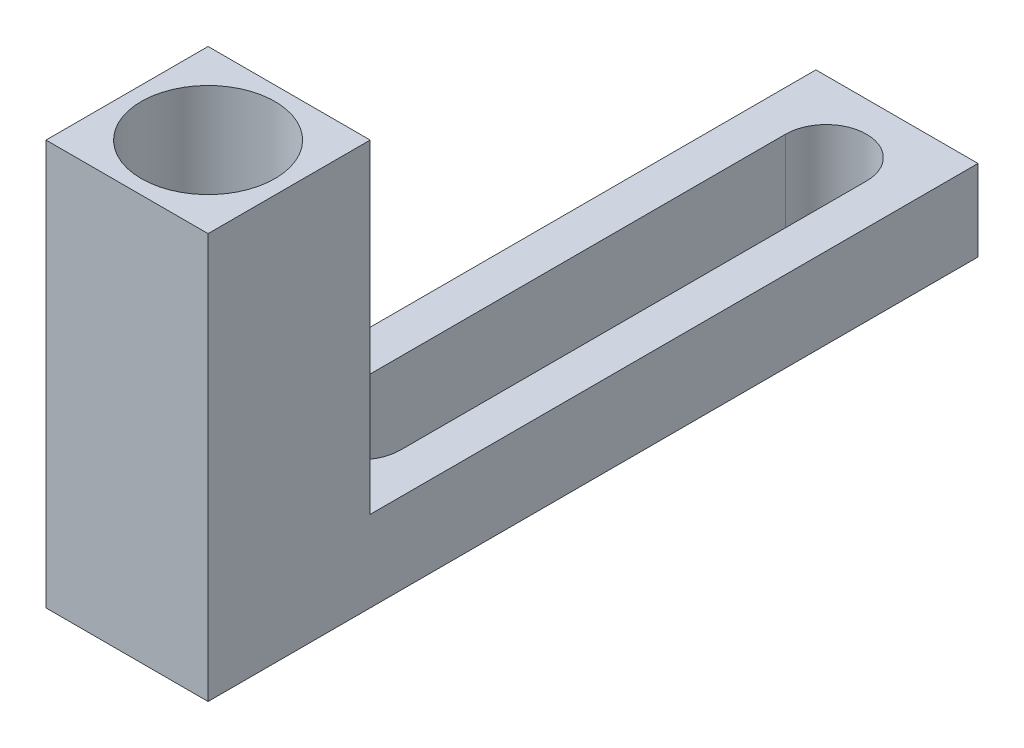
SolidWorks part; units mm, degrees
ref_plane "Front Plane" through (0, 0, 0) normal (0, 0, 1) x (1, 0, 0)
ref_plane "Top Plane" through (0, 0, 0) normal (0, 1, 0) x (1, 0, 0)
ref_plane "Right Plane" through (0, 0, 0) normal (1, 0, 0) x (0, 0, -1)
sketch "Sketch2" plane through (0, 0, 0) normal (0, 1, 0) x (1, 0, 0)
  line L1 (-4, -15) -> (4, -15)
  line L2 (-4, -15) -> (-4, 15)
  line L3 (-4, 15) -> (4, 15)
  line L4 (4, -15) -> (4, 15)
  line L5 (-4, -15) -> (4, 15) construction
  line L6 (-4, 15) -> (4, -15) construction
  point P0 (0, 0)
extrude "Boss-Extrude1" add sketch "Sketch2" along normal blind 4
sketch "Sketch3" plane through (0, 0, 0) normal (0, 1, 0) x (1, 0, 0)
  line L0 (0, -11.5) -> (0, 11.5) construction
  line L1 (-2, -11.5) -> (-2, 11.5)
  line L2 (2, -11.5) -> (2, 11.5)
  arc A0 (-2, -11.5) -> (2, -11.5) centre (0, -11.5) ccw
  arc A1 (2, 11.5) -> (-2, 11.5) centre (0, 11.5) ccw
  point P2 (0, 0)
extrude "Cut-Extrude1" cut sketch "Sketch3" along normal through all
sketch "Sketch4" plane through (0, 0, 0) normal (0, 1, 0) x (1, 0, 0)
  line L0 (4, -15) -> (4, 15) construction
  line L1 (-4, -15) -> (4, -15)
  line L2 (-4, -15) -> (-4, -23)
  line L3 (-4, -23) -> (4, -23)
  line L4 (4, -15) -> (4, -23)
extrude "Boss-Extrude2" add sketch "Sketch4" along normal blind 20
ref_plane "Plane1" through (0, 20, 0) normal (0, 1, 0) x (1, 0, 0)
sketch "Sketch5" plane through (0, 20, 0) normal (0, 1, 0) x (1, 0, 0)
  line L0 (-4, -19) -> (0, -19) construction
  line L1 (-4, -15) -> (-4, -23) construction
  circle A0 centre (0, -19) radius 3.3
extrude "Cut-Extrude2" cut sketch "Sketch5" against normal offset from surface (15.5 mm away) 4.5 up to face at (0, 0, 4)
ref_plane "Plane2" through (-4, 0, 0) normal (-1, 0, 0) x (0, 0, 1)
sketch "Sketch6" plane through (-4, 0, 0) normal (-1, 0, 0) x (0, 0, 1)
  line L0 (23, 0) -> (23, 6) construction
  line L1 (23, 20) -> (23, 0) construction
  line L2 (19.5, 6) -> (18.5, 6) construction
  line L3 (23, 6) -> (19, 6) construction
  line L4 (19.5, 4.5) -> (18.5, 4.5)
  line L5 (19.5, 7.5) -> (18.5, 7.5)
  arc A0 (19.5, 4.5) -> (19.5, 7.5) centre (19.5, 6) ccw
  arc A1 (18.5, 7.5) -> (18.5, 4.5) centre (18.5, 6) ccw
  point P7 (19, 6)
  point P13 (0, 0)
  point P14 (0, 0)
  point P15 (0, 0)
extrude "Cut-Extrude3" cut sketch "Sketch6" against normal up to next
